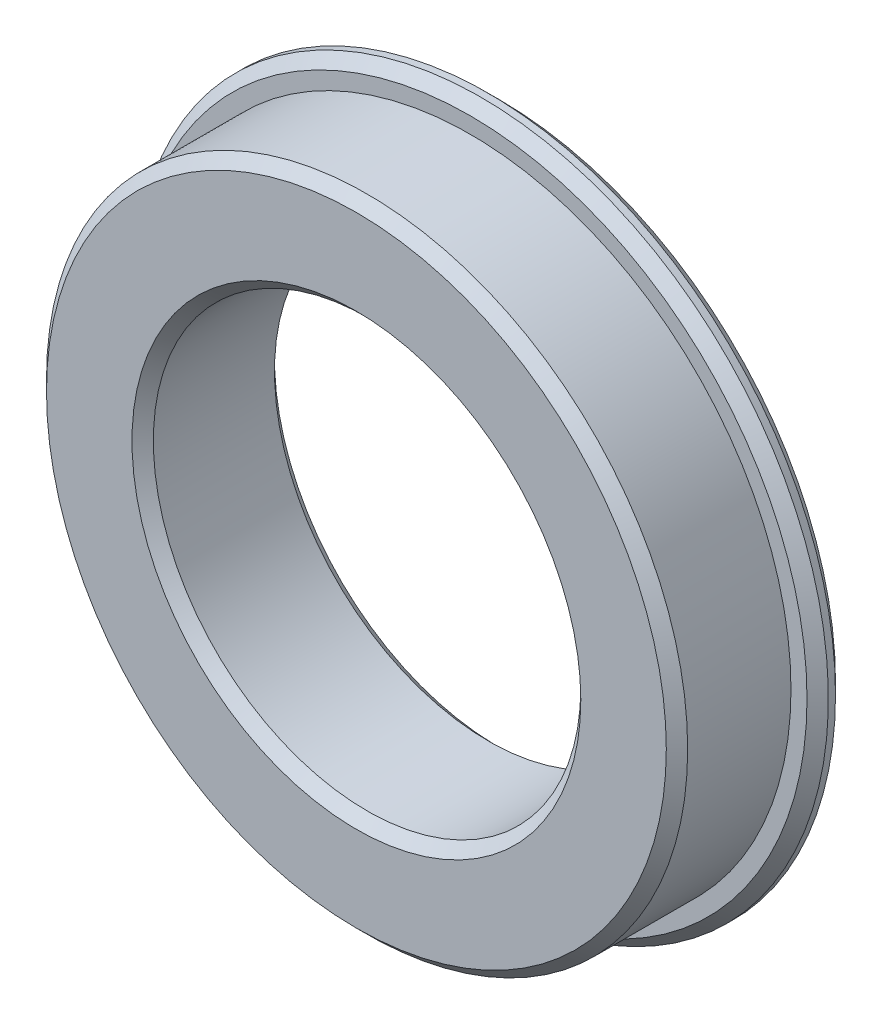
SolidWorks part; units mm, degrees
ref_plane "前视基准面" through (0, 0, 0) normal (0, 0, 1) x (1, 0, 0)
ref_plane "上视基准面" through (0, 0, 0) normal (0, 1, 0) x (1, 0, 0)
ref_plane "右视基准面" through (0, 0, 0) normal (1, 0, 0) x (0, 0, -1)
sketch "草图1" plane through (0, 0, 0) normal (0, 0, 1) x (1, 0, 0)
  circle A0 centre (0, 0) radius 6
  circle A1 centre (0, 0) radius 9
  dimension "D1" = 12
  dimension "D2" = 18
extrude "凸台-拉伸1" add sketch "草图1" along normal blind 4
sketch "草图2" plane through (0, 0, 0) normal (0, 0, -1) x (-1, 0, 0)
  circle A0 centre (0, 0) radius 9.75
  circle A1 centre (0, 0) radius 9 construction
  circle A2 centre (0, 0) radius 9
  dimension "D1" = 19.5
extrude "凸台-拉伸2" add sketch "草图2" against normal blind 0.8
chamfer "倒角1" distance 0.3 angle 45 5 edges at (6, 0, 4) (6, 0, 0) (-9.75, 0, 0.8) (-9.75, 0, 0) (9, 0, 4)
